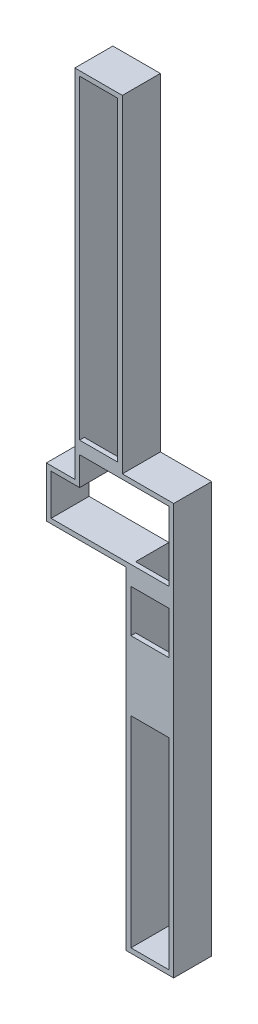
SolidWorks part; units mm, degrees
ref_plane "Alzado" through (0, 0, 0) normal (0, 0, 1) x (1, 0, 0)
ref_plane "Planta" through (0, 0, 0) normal (0, 1, 0) x (1, 0, 0)
ref_plane "Vista lateral" through (0, 0, 0) normal (1, 0, 0) x (0, 0, -1)
sketch "Croquis1" plane through (0, 0, 0) normal (0, 0, 1) x (1, 0, 0)
  line L0 (-273.5468, 0) -> (-273.5468, 7500)
  line L1 (-273.5468, 0) -> (-873.5468, 0)
  line L2 (-873.5468, 0) -> (-873.5468, -860)
  line L3 (-873.5468, -860) -> (-373.5468, -860)
  line L4 (-373.5468, -860) -> (806.4532, -860)
  line L5 (806.4532, -860) -> (806.4532, -7850)
  line L6 (526.4532, 7500) -> (526.4532, 600)
  line L7 (1606.4532, 499.6482) -> (1606.4532, 600)
  line L8 (1606.4532, 0) -> (1606.4532, -2193.6851)
  line L9 (-273.5468, 7500) -> (526.4532, 7500)
  line L10 (806.4532, -7850) -> (1606.4532, -7850)
  line L11 (1606.4532, -7850) -> (1606.4532, -2193.6851)
  line L12 (1606.4532, -7950) -> (1706.4532, -7950)
  line L13 (1706.4532, -7950) -> (1706.4532, 99.6482)
  line L14 (1606.4532, 399.6482) -> (1606.4532, 0)
  line L15 (626.4532, 700) -> (626.4532, 7600)
  line L16 (626.4532, 7600) -> (-373.5468, 7600)
  line L17 (-373.5468, 7600) -> (-373.5468, 100)
  line L18 (706.4532, -960) -> (-973.5468, -960)
  line L19 (-973.5468, -960) -> (-973.5468, 100)
  line L20 (-973.5468, 100) -> (-373.5468, 100)
  line L21 (706.4532, -960) -> (706.4532, -7950)
  line L22 (706.4532, -7950) -> (1606.4532, -7950)
  line L23 (1606.4532, 600) -> (526.4532, 600)
  line L24 (1706.4532, 99.6482) -> (1706.4532, 499.6482)
  line L25 (1606.4532, 399.6482) -> (1606.4532, 499.6482)
  line L26 (1706.4532, 499.6482) -> (1706.4532, 599.6482)
  line L27 (1706.4532, 599.6482) -> (1706.4532, 700)
  line L28 (1706.4532, 700) -> (626.4532, 700)
  point P22 (1166.4532, 700)
  dimension "D1" = 800
  dimension "D2" = 600
  dimension "D3" = 100
  dimension "D4" = 6990
  dimension "D5" = 600
  dimension "D6" = 100
  dimension "D7" = 100
  dimension "D8" = 100
  dimension "D9" = 100
  dimension "D14" = 800
  dimension "D15" = 100
  dimension "D16" = 100
  dimension "D17" = 100
  dimension "D18" = 100
extrude "Saliente-Extruir1" add sketch "Croquis1" along normal blind 800
sketch "Croquis2" plane through (0, 0, 800) normal (0, 0, 1) x (1, 0, 0)
  line L0 (806.4532, -860) -> (1606.4532, -860)
  line L1 (1606.4532, -7850) -> (1606.4532, 600) construction
  line L2 (1606.4532, -860) -> (1606.4532, -1260)
  line L3 (1606.4532, -1260) -> (806.4532, -1260)
  line L4 (806.4532, -860) -> (806.4532, -7850) construction
  line L5 (806.4532, -1260) -> (806.4532, -860)
  dimension "D1" = 400
extrude "Saliente-Extruir2" add sketch "Croquis2" against normal blind 100
sketch "Croquis3" plane through (0, 0, 800) normal (0, 0, 1) x (1, 0, 0)
  line L0 (806.4532, -2160) -> (1606.4532, -2160)
  line L1 (806.4532, -1260) -> (806.4532, -7850) construction
  line L2 (1606.4532, -7850) -> (1606.4532, -1260) construction
  line L3 (806.4532, -1260) -> (1606.4532, -1260) construction
  line L4 (1606.4532, -2160) -> (1606.4532, -3618.3398)
  line L5 (1606.4532, -3618.3398) -> (806.4532, -3618.3398)
  line L6 (806.4532, -3618.3398) -> (806.4532, -2160)
  dimension "D1" = 900
extrude "Saliente-Extruir3" add sketch "Croquis3" against normal blind 100
sketch "Croquis4" plane through (0, 0, 800) normal (0, 0, 1) x (1, 0, 0)
  line L0 (526.4532, 600) -> (-273.5468, 600)
  line L1 (-273.5468, 7500) -> (-273.5468, 0) construction
  line L2 (-273.5468, 600) -> (-273.5468, 865)
  line L3 (-273.5468, 865) -> (526.4532, 865)
  line L4 (526.4532, 600) -> (526.4532, 7500) construction
  line L5 (526.4532, 865) -> (526.4532, 600)
  dimension "D1" = 265
extrude "Saliente-Extruir4" add sketch "Croquis4" against normal blind 100
